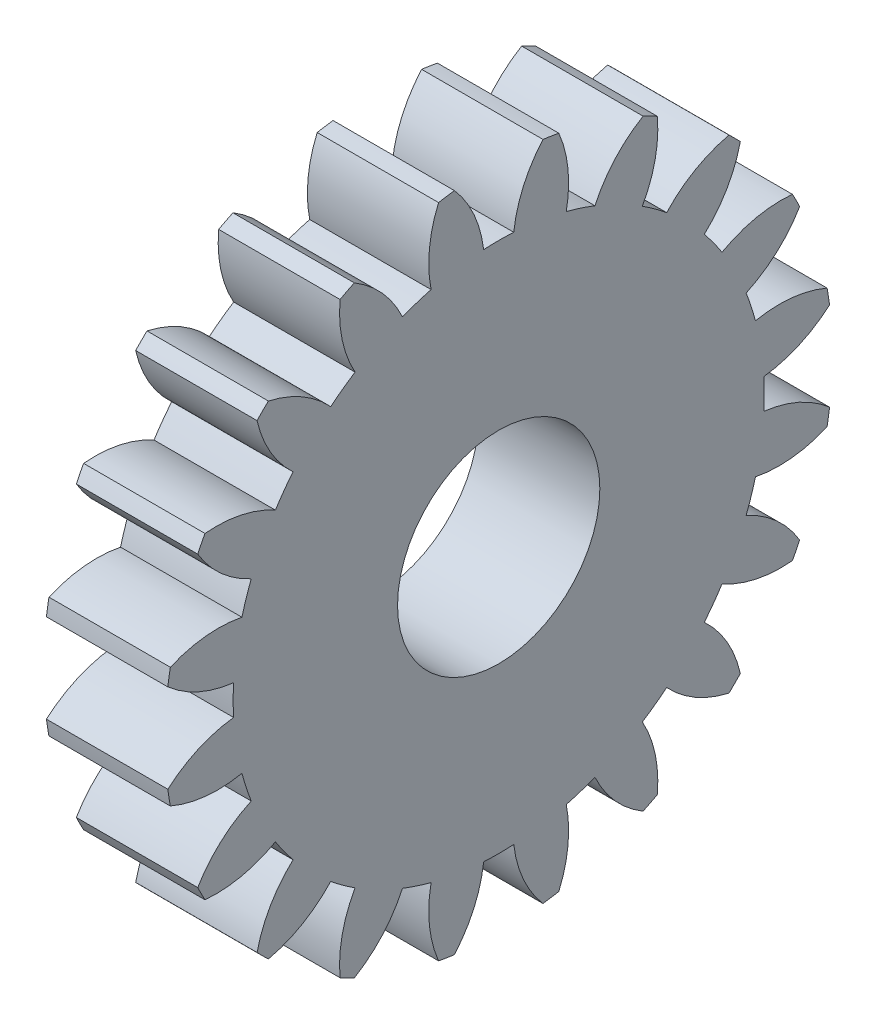
SolidWorks part; units mm, degrees
ref_plane "Plane1" through (0, 0, 0) normal (0, 0, 1) x (1, 0, 0)
ref_plane "Plane2" through (0, 0, 0) normal (0, 1, 0) x (1, 0, 0)
ref_plane "Plane3" through (0, 0, 0) normal (1, 0, 0) x (0, 0, -1)
sketch "HoldingSke" plane through (0, 0, 0) normal (0, 1, 0) x (1, 0, 0)
  line L0 (0, 0) -> (0.6265, -0.228)
  line L1 (-15, 0) -> (100, 0) construction
  line L2 (0, 0) -> (-2.1039, 2.3779)
  line L3 (0, 0) -> (-11.863, 4.5341)
  line L4 (0, 0) -> (8.1152, 2.9537)
  line L5 (0, 0) -> (-46.8476, -17.4728)
  line L6 (0, 0) -> (-4.9738, -3.3558)
  line L7 (-2.1039, 2.3779) -> (8.6586, 51.2059)
  line L8 (-76.2, 54.61) -> (-74.4, 54.61)
  line L9 (-71.009, 38.7566) -> (-53.1078, 45.2721)
  line L10 (-76.2, 71.12) -> (104.1128, 71.12)
  line L11 (0, 0) -> (-6, 0)
  line L12 (-76.2, 101.6) -> (-76.147, 101.6)
  line L13 (24.9733, 27.94) -> (52.9518, 28.4284)
  line L14 (24.9733, 27.94) -> (24.9743, 27.94)
  line L15 (24.9733, 27.94) -> (100.4006, 29.5858)
  line L16 (-63.627, -1.5) -> (-12.827, -1.5)
  circle A0 centre (0, 0) radius 5
  circle A1 centre (0, 0) radius 13.124
  circle A2 centre (0, 0) radius 37.5
  circle A3 centre (0, 0) radius 5
  dimension "MHD" = 26.248
  dimension "Hub_dia" = 75
  dimension "Bore" = 10
  dimension "MBD" = 10
  dimension "Num_teeth" = 20
  dimension "Pitch" = 0.6667
  dimension "Overall_len" = 50
  dimension "Show_teeth" = 20
  dimension "Thickness" = 6
  dimension "OAL" = 50.0001
  dimension "T_dim" = 1.8
  dimension "Ap" = 20
  dimension "H" = 19.05
  dimension "Pitch_radius" = 180.3128
  dimension "Width" = 6
  dimension "Backlash" = 0.053
  dimension "Addendum_fac" = 1
  dimension "Dedendum_fac" = 1.25
  dimension "Clearance_fac" = 0.25
  dimension "Dedendum_add" = 0.001
  dimension "Module" = 1.5
sketch "BasProSke" plane through (0, 0, 0) normal (0, 1, 0) x (1, 0, 0)
  line L0 (-10, 0) -> (60, 0) construction
  line L1 (0, 0) -> (0, 16.5)
  line L2 (0, 0) -> (6, 0)
  line L3 (6, 0) -> (6, 16.5)
  line L4 (6, 16.5) -> (0, 16.5)
  dimension "Thickness" = 6
  dimension "Diameter" = 33
revolve "Base-Revolve" add sketch "BasProSke" angle 360 about L0
sketch "TooCutSke" plane through (0, 0, 0) normal (1, 0, 0) x (0, 0, -1)
  line L1 (0, 0) -> (0, 107) construction
  line L2 (0, 0) -> (-1.2696, 14.9462) construction
  line L3 (0, 0) -> (-4.6808, 29.5532) construction
  line L4 (-1.2696, 14.9462) -> (-2.3404, 14.7766) construction
  arc A0 (0.7438, 13.1029) -> (-0.7438, 13.1029) centre (0, 0) ccw
  arc A1 (2.21, 16.377) -> (-2.21, 16.377) centre (0, 0) ccw
  circle A2 centre (0, 0) radius 15 construction
  circle A3 centre (0, 0) radius 14.0954 construction
  arc A4 (-0.7438, 13.1029) -> (-2.21, 16.377) centre (-6.7025, 12.3999) ccw
  arc A5 (2.21, 16.377) -> (0.7438, 13.1029) centre (6.7025, 12.3999) ccw
  dimension "Root_dia" = 26.248
  dimension "Overcut_dia" = 33.0508
  dimension "Pitch_dia" = 30
  dimension "Base_dia" = 28.1908
  dimension "Flank_rad" = 6
  dimension "Half_ang" = 9
  dimension "Half_CT" = 1.0841
extrude "ToothCut" cut sketch "TooCutSke" along normal through all
fillet "Breaks" [suppressed] radius 0.03
fillet "RootFillets" [suppressed] radius 0.376
pattern_circular "TeethCuts" count 20 every 18 about axis through (-10, 0, 0) along (1, 0, 0) of "ToothCut", "RootFillets", "Breaks"
sketch "HubNeaOneSke" plane through (0, 0, 0) normal (-1, 0, 0) x (0, 0, 1)
  circle A0 centre (0, 0) radius 13.124
  dimension "Diameter" = 26.248
extrude "HubNearOne" [suppressed] add sketch "HubNeaOneSke" along normal blind 44.0001
sketch "HubNeaBotSke" plane through (0, 0, 0) normal (-1, 0, 0) x (0, 0, 1)
  circle A0 centre (0, 0) radius 13.124
  dimension "Diameter" = 26.248
extrude "HubNearBoth" [suppressed] add sketch "HubNeaBotSke" along normal blind 22
ref_plane "FarPln" through (6, 0, 0) normal (1, 0, 0) x (0, 0, -1)
sketch "HubFarSke" plane through (6, 0, 0) normal (1, 0, 0) x (0, 0, -1)
  circle A0 centre (0, 0) radius 13.124
  dimension "Diameter" = 26.248
extrude "HubFar" [suppressed] add sketch "HubFarSke" along normal blind 22
sketch "BorSke" plane through (0, 0, 0) normal (1, 0, 0) x (0, 0, -1)
  circle A0 centre (0, 0) radius 5
  dimension "Diameter" = 10
extrude "Bore" cut sketch "BorSke" along normal mid plane 100.0001
sketch "KeySke" plane through (0, 0, 0) normal (1, 0, 0) x (0, 0, -1)
  line L0 (-2, 0) -> (-2, 6.8)
  line L1 (-2, 6.8) -> (2, 6.8)
  line L2 (2, 6.8) -> (2, 0)
  line L3 (0, 0) -> (0, 34) construction
  line L4 (-2, 0) -> (2, 0)
  dimension "Offset" = 6.8
  dimension "Width" = 4
extrude "Keyway" [suppressed] cut sketch "KeySke" along normal mid plane 100.0001
pattern_circular "Keyway2" [suppressed] count 2 every 90 about axis through (-10, 0, 0) along (1, 0, 0)
sketch "Esquisse1" plane through (6, 0, 0) normal (1, 0, 0) x (0, 0, -1)
  circle A0 centre (0, 0) radius 15
equation "' \"Module@HoldingSke\" = 6.35"
equation "' \"Num_teeth@HoldingSke\" = 12"
equation "' \"Ap@HoldingSke\" =  20"
equation "' \"Ap@HoldingSke\" = 20"
equation "' \"Width@HoldingSke\" = 0.5 * 25.4"
equation "' \"Hub_dia@HoldingSke\"= 1 * 25.4"
equation "' \"Hub_dia@HoldingSke\" = 1 * 25.4"
equation "' \"Overall_len@HoldingSke\" = 1.0 * 25.4"
equation "' \"Bore@HoldingSke\" = 0.75 * 25.4"
equation "' \"T_dim@HoldingSke\" = 0.1 * 25.4"
equation "' \"Width@KeySke\" = 0.25 * 25.4"
equation "' \"Show_teeth@HoldingSke\" = 13"
equation "' \"Backlash@HoldingSke\" = 0.009 * 25.4"
equation "' \"Addendum_fac@HoldingSke\" = 1.0"
equation "' \"Dedendum_fac@HoldingSke\" = 1.25"
equation "' \"Dedendum_add@HoldingSke\" = 0.00005 * 25.4"
equation "' \"Clearance_fac@HoldingSke\" = 0.25"
equation "\"Pitch@HoldingSke\" = 1 / \"Module@HoldingSke\""
equation "\"Overcut_dia@TooCutSke\" = (\"Num_teeth@HoldingSke\" + 2 * \"Addendum_fac@HoldingSke\") / \"Pitch@HoldingSke\" + 0.002 * 25.4"
equation "\"Pitch_dia@TooCutSke\" = \"Num_teeth@HoldingSke\" / \"Pitch@HoldingSke\""
equation "\"Base_dia@TooCutSke\" = \"Num_teeth@HoldingSke\" / \"Pitch@HoldingSke\" * cos((\"Ap@HoldingSke\"  * 3.14159265 / 180))"
equation "\"Root_dia@TooCutSke\" = (\"Num_teeth@HoldingSke\" + 2) / \"Pitch@HoldingSke\" - 2 * (\"Addendum_fac@HoldingSke\" + \"Dedendum_fac@HoldingSke\") / \"Pitch@HoldingSke\" - \"Dedendum_add@HoldingSke\" * 2"
equation "\"Half_ang@TooCutSke\" = 180 / \"Num_teeth@HoldingSke\""
equation "\"Half_CT@TooCutSke\" = \"Num_teeth@HoldingSke\" / \"Pitch@HoldingSke\" * sin((3.14159265 / 2 / \"Num_teeth@HoldingSke\")) / 2 - 7 * \"Backlash@HoldingSke\" / 4"
equation "\"Flank_rad@TooCutSke\" = \"Num_teeth@HoldingSke\" / \"Pitch@HoldingSke\" / 5"
equation "\"Radius@RootFillets\" = \"Clearance_fac@HoldingSke\" / \"Pitch@HoldingSke\" + \"Dedendum_add@HoldingSke\""
equation "\"Break_rad@Breaks\" = 0.02 / \"Pitch@HoldingSke\""
equation "\"Thickness@HoldingSke\" = \"Width@HoldingSke\""
equation "\"OAL@HoldingSke\" = \"Thickness@HoldingSke\""
equation "\"MHD@HoldingSke\" = (\"Num_teeth@HoldingSke\" + 2) / \"Pitch@HoldingSke\" - 2 * (\"Addendum_fac@HoldingSke\" + \"Dedendum_fac@HoldingSke\")  / \"Pitch@HoldingSke\" - \"Dedendum_add@HoldingSke\" * 2"
equation "\"MBD@HoldingSke\" = (\"Num_teeth@HoldingSke\" + 2) / \"Pitch@HoldingSke\" - 2 * (\"Addendum_fac@HoldingSke\" + \"Dedendum_fac@HoldingSke\")  / \"Pitch@HoldingSke\" - \"Dedendum_add@HoldingSke\" * 2 - 0.002 * 25.4"
equation "\"MHD@HoldingSke\" = ((sgn( \"MHD@HoldingSke\" - \"Hub_dia@HoldingSke\" )-1)*( \"MHD@HoldingSke\" - \"Hub_dia@HoldingSke\" ))/-2+ \"Hub_dia@HoldingSke\""
equation "\"MBD@HoldingSke\" = ((sgn( \"MBD@HoldingSke\" - \"Bore@HoldingSke\" )-1)*( \"MBD@HoldingSke\" - \"Bore@HoldingSke\" ))/-2+ \"Bore@HoldingSke\""
equation "\"OAL@HoldingSke\" = ((sgn( \"OAL@HoldingSke\" - \"Overall_len@HoldingSke\" )+1)*( \"OAL@HoldingSke\" - \"Overall_len@HoldingSke\" ))/2 + \"Overall_len@HoldingSke\" + 0.000002 * 25.4"
equation "\"Num_teeth@TeethCuts\" = int( \"Show_teeth@HoldingSke\" ) + 1"
equation "\"Num_teeth@TeethCuts\" = ((sgn( \"Num_teeth@TeethCuts\" - \"Num_teeth@HoldingSke\" )-1)*( \"Num_teeth@TeethCuts\" - \"Num_teeth@HoldingSke\" ))/-2+ \"Num_teeth@HoldingSke\""
equation "\"Num_teeth@TeethCuts\" = ((sgn( \"Num_teeth@TeethCuts\" - 2.0)+1)*( \"Num_teeth@TeethCuts\" - 2.0))/2 +2.0"
equation "\"Angle@TeethCuts\" = 360.0 / \"Num_teeth@HoldingSke\""
equation "\"Diameter@BasProSke\" = (\"Num_teeth@HoldingSke\" + 2 * \"Addendum_fac@HoldingSke\") / \"Pitch@HoldingSke\""
equation "\"Thickness@BasProSke\"  = \"Thickness@HoldingSke\""
equation "' \"Fillet_rad@BasProSke\" =  \"Thickness@HoldingSke\" * 0.05"
equation "' \"Fillet_rad@BasProSke\" = \"Thickness@HoldingSke\" * 0.05"
equation "\"MHD@HoldingSke\" = ((sgn( \"MHD@HoldingSke\" - \"Root_dia@TooCutSke\" )-1)*( \"MHD@HoldingSke\" - \"Root_dia@TooCutSke\" ))/-2+ \"Root_dia@TooCutSke\""
equation "\"Diameter@HubNeaOneSke\" = \"MHD@HoldingSke\""
equation "\"Length@HubNearOne\" = \"OAL@HoldingSke\" - \"Thickness@BasProSke\""
equation "\"Diameter@HubNeaBotSke\" = \"MHD@HoldingSke\""
equation "\"Length@HubNearBoth\" = ( \"OAL@HoldingSke\" - \"Thickness@BasProSke\" ) / 2.0"
equation "\"Thickness@FarPln\" = \"Thickness@BasProSke\""
equation "\"Diameter@HubFarSke\" = \"MHD@HoldingSke\""
equation "\"Length@HubFar\" = ( \"OAL@HoldingSke\" - \"Thickness@BasProSke\" ) / 2.0"
equation "\"Diameter@BorSke\" = \"MBD@HoldingSke\""
equation "\"D1@Bore\" = \"OAL@HoldingSke\" * 2.0"
equation "\"D1@Keyway\" = \"OAL@HoldingSke\" * 2.0"
equation "\"Offset@KeySke\" = \"T_dim@HoldingSke\" + \"MBD@HoldingSke\" / 2.0"
